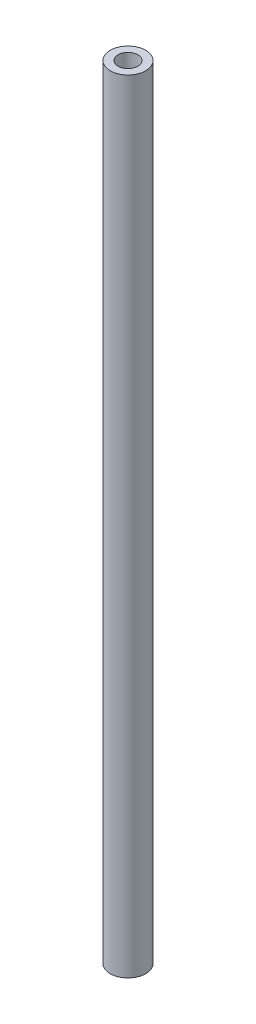
SolidWorks part; units mm, degrees
ref_plane "Front Plane" through (0, 0, 0) normal (0, 0, 1) x (1, 0, 0)
ref_plane "Top Plane" through (0, 0, 0) normal (0, 1, 0) x (1, 0, 0)
ref_plane "Right Plane" through (0, 0, 0) normal (1, 0, 0) x (0, 0, -1)
sketch "Sketch2" plane through (0, 0, 0) normal (0, 1, 0) x (1, 0, 0)
  circle A0 centre (0, 0) radius 11.35
extrude "Boss-Extrude1" add sketch "Sketch2" along normal blind 500
hole_wizard "Hole2" positions "Sketch5" profile "Sketch6" legacy end condition through all
sketch "Sketch5" plane through (0, 0, 0) normal (0, -1, 0) x (-1, 0, 0)
  point P0 (0, 0)
sketch "Sketch6" plane through (0, 0, 0) normal (1, 0, 0) x (0, 0, -1)
  line L0 (0, 0) -> (0, 500)
  line L1 (0, 500) -> (6.35, 500)
  line L2 (6.35, 500) -> (6.35, 0)
  line L3 (6.35, 0) -> (0, 0)
  line L4 (0, 110) -> (0, -10) construction
  dimension "Diameter" = 12.7
  dimension "Depth" = 500
